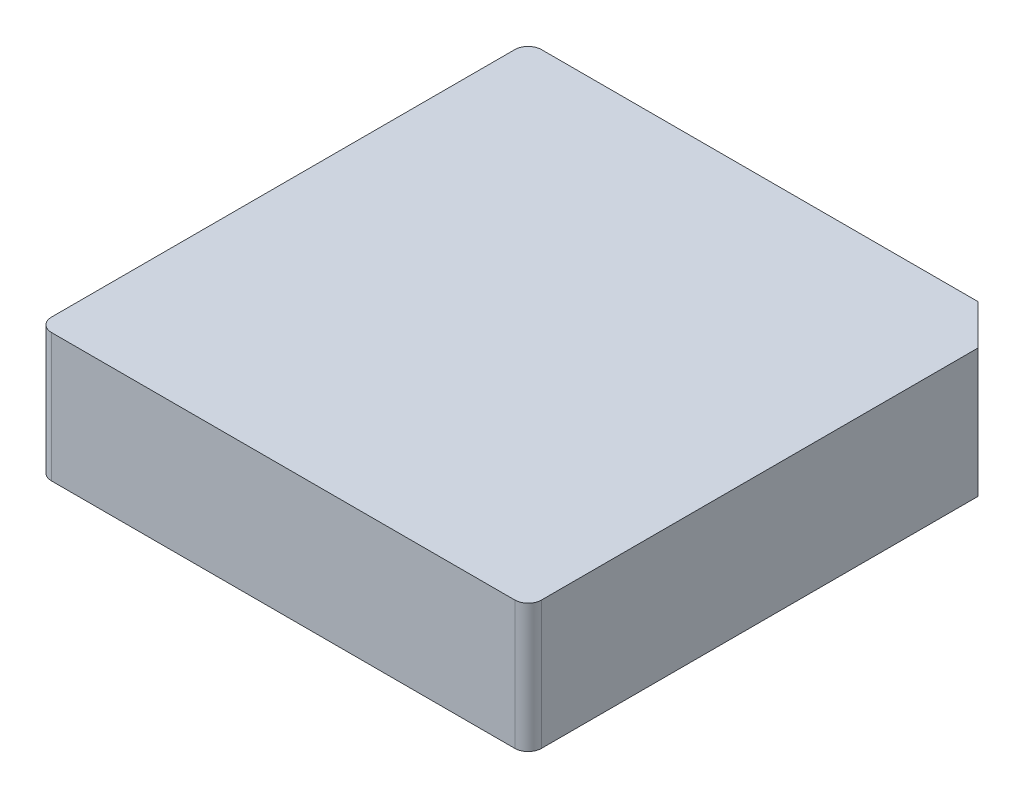
SolidWorks part; units mm, degrees
ref_plane "Front Plane" through (0, 0, 0) normal (0, 0, 1) x (1, 0, 0)
ref_plane "Top Plane" through (0, 0, 0) normal (0, 1, 0) x (1, 0, 0)
ref_plane "Right Plane" through (0, 0, 0) normal (1, 0, 0) x (0, 0, -1)
sketch "Sketch1" plane through (0, 0, 0) normal (0, 1, 0) x (1, 0, 0)
  line L0 (7.65, 9.15) -> (9.15, 7.65)
  line L1 (-9.15, -9.15) -> (9.15, -9.15)
  line L2 (-9.15, -9.15) -> (-9.15, 9.15)
  line L3 (-9.15, 9.15) -> (9.15, 9.15)
  line L4 (9.15, -9.15) -> (9.15, 9.15)
  line L5 (-9.15, -9.15) -> (9.15, 9.15) construction
  line L6 (-9.15, 9.15) -> (9.15, -9.15) construction
  point P0 (0, 0)
  dimension "D1" = 18.3
  dimension "D2" = 18.3
  dimension "D3" = 1.5
extrude "Boss-Extrude1" add sketch "Sketch1" along normal blind 4.8 contours L1 L4 L0 L3 L2
fillet "Fillet1" radius 0.5 3 edges at (-9.15, 2.4, -9.15) (-9.15, 2.4, 9.15) (9.15, 2.4, 9.15)
sketch "Sketch2" plane through (0, 0, 0) normal (0, -1, 0) x (1, 0, 0)
  circle A0 centre (0, 1.8) radius 0.475
  dimension "D2" = 0.95
  dimension "D1" = 1.8
extrude "Boss-Extrude2" add sketch "Sketch2" along normal blind 1.9
